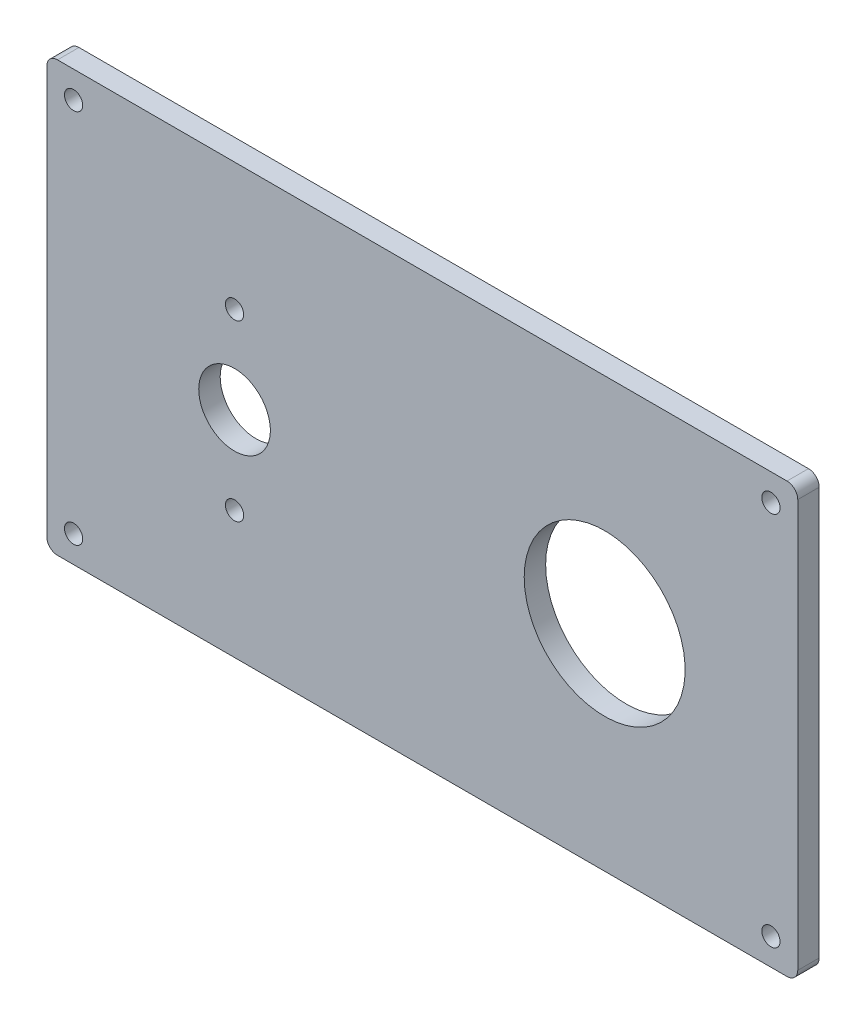
SolidWorks part; units mm, degrees
ref_plane "Front Plane" through (0, 0, 0) normal (0, 0, 1) x (1, 0, 0)
ref_plane "Top Plane" through (0, 0, 0) normal (0, 1, 0) x (1, 0, 0)
ref_plane "Right Plane" through (0, 0, 0) normal (1, 0, 0) x (0, 0, -1)
sketch "Sketch1" plane through (0, 0, 0) normal (0, 0, 1) x (1, 0, 0)
  line L1 (-1.1094, 38.5389) -> (138.8906, 38.5389)
  line L2 (-1.1094, 38.5389) -> (-1.1094, -41.4611)
  line L3 (-1.1094, -41.4611) -> (138.8906, -41.4611)
  line L4 (138.8906, 38.5389) -> (138.8906, -41.4611)
  dimension "D1" = 80
  dimension "D2" = 140
extrude "Boss-Extrude1" add sketch "Sketch1" along normal blind 4
sketch "Sketch2" plane through (0, 0, 0) normal (0, 0, -1) x (-1, 0, 0)
  line L0 (1.1094, -41.4611) -> (-138.8906, -41.4611) construction
  line L1 (1.1094, 38.5389) -> (1.1094, -41.4611) construction
  line L2 (-138.8906, 38.5389) -> (1.1094, 38.5389) construction
  line L4 (-138.8906, -41.4611) -> (-138.8906, 38.5389) construction
  circle A0 centre (-133.8906, 33.5389) radius 1.7
  circle A1 centre (-3.8906, 33.5389) radius 1.7
  circle A2 centre (-133.8906, -36.4611) radius 1.7
  circle A3 centre (-3.8906, -36.4611) radius 1.7
  circle A4 centre (-33.8906, -1.4611) radius 6.675
  circle A5 centre (-102.8906, -1.4611) radius 15
  circle A6 centre (-3.8906, -1.4611) radius 1.6
  circle A7 centre (-33.8906, -17.6811) radius 1.7
  circle A8 centre (-33.8906, 14.7589) radius 1.7
  dimension "D1" = 5
  dimension "D9" = 13.35
  dimension "D12" = 3.4
  dimension "D13" = 3.4
  dimension "D14" = 3.4
  dimension "D15" = 3.4
  dimension "D16" = 30
  dimension "D17" = 35
  dimension "D18" = 40
  dimension "D19" = 5
  dimension "D21" = 16.22
  dimension "D22" = 16.22
  dimension "D23" = 3.4
  dimension "D2" = 5
  dimension "D3" = 5
  dimension "D4" = 5
  dimension "D5" = 5
  dimension "D6" = 5
  dimension "D7" = 5
  dimension "D8" = 5
  dimension "D10" = 36
  dimension "D11" = 69
  dimension "D20" = 40
extrude "Cut-Extrude1" cut sketch "Sketch2" against normal blind 4 contours A4 | A8 | A7 | A3 | A2 | A0 | A1 | A5
fillet "Fillet1" radius 2 4 edges at (138.8906, -41.4611, 2) (-1.1094, -41.4611, 2) (-1.1094, 38.5389, 2) (138.8906, 38.5389, 2)
